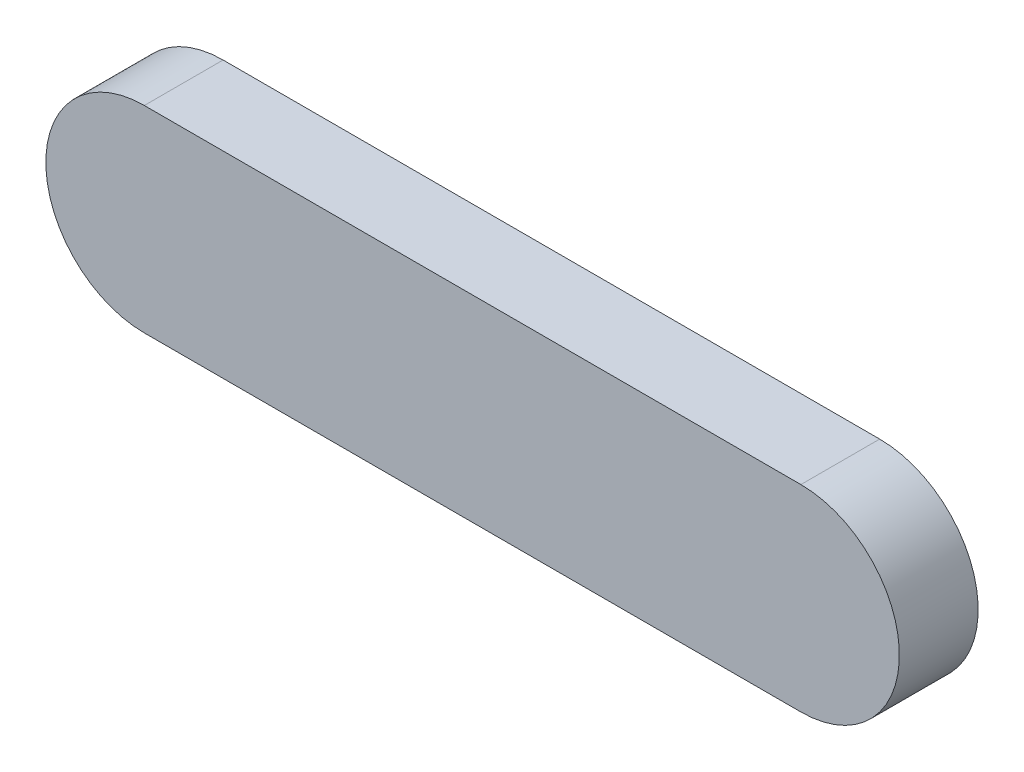
SolidWorks part; units mm, degrees
ref_plane "前视基准面" through (0, 0, 0) normal (0, 0, 1) x (1, 0, 0)
ref_plane "上视基准面" through (0, 0, 0) normal (0, 1, 0) x (1, 0, 0)
ref_plane "右视基准面" through (0, 0, 0) normal (1, 0, 0) x (0, 0, -1)
sketch "草图1" plane through (0, 0, 0) normal (0, 0, 1) x (1, 0, 0)
  line L1 (-50, 25) -> (50, 25)
  line L2 (-50, -5) -> (50, -5)
  arc A0 (-50, 25) -> (-50, -5) centre (-50, 10) ccw
  arc A1 (50, -5) -> (50, 25) centre (50, 10) ccw
  point P4 (0, 0)
  dimension "D2" = 30
  dimension "D1" = 100
extrude "凸台-拉伸1" add sketch "草图1" along normal blind 12
sketch "草图2" plane through (0, 0, 0) normal (0, 0, -1) x (-1, 0, 0)
  circle A0 centre (-50, 10) radius 5
